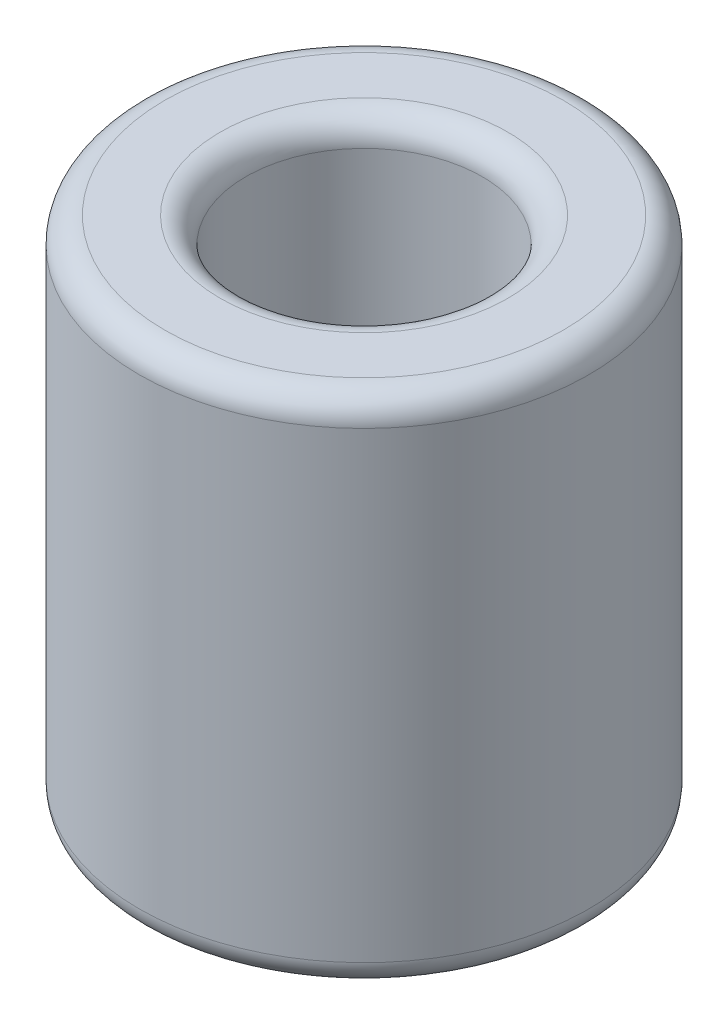
SolidWorks part; units mm, degrees
material "Polyetheretherketone (PEEK)"
ref_plane "Front" through (0, 0, 0) normal (0, 0, 1) x (1, 0, 0)
ref_plane "Top" through (0, 0, 0) normal (0, 1, 0) x (1, 0, 0)
ref_plane "Right" through (0, 0, 0) normal (1, 0, 0) x (0, 0, -1)
sketch "Sketch1" plane through (0, 0, 0) normal (0, 1, 0) x (1, 0, 0)
  circle A0 centre (0, 0) radius 4.375
  circle A1 centre (0, 0) radius 2.3
  dimension "D1" = 8.75
  dimension "D2" = 4.6
extrude "Boss-Extrude1" add sketch "Sketch1" along normal blind 10
fillet "Fillet1" radius 0.5 4 edges at (0, 0, 2.3) (0, 0, 4.375) (0, 10, 2.3) (0, 10, 4.375)
